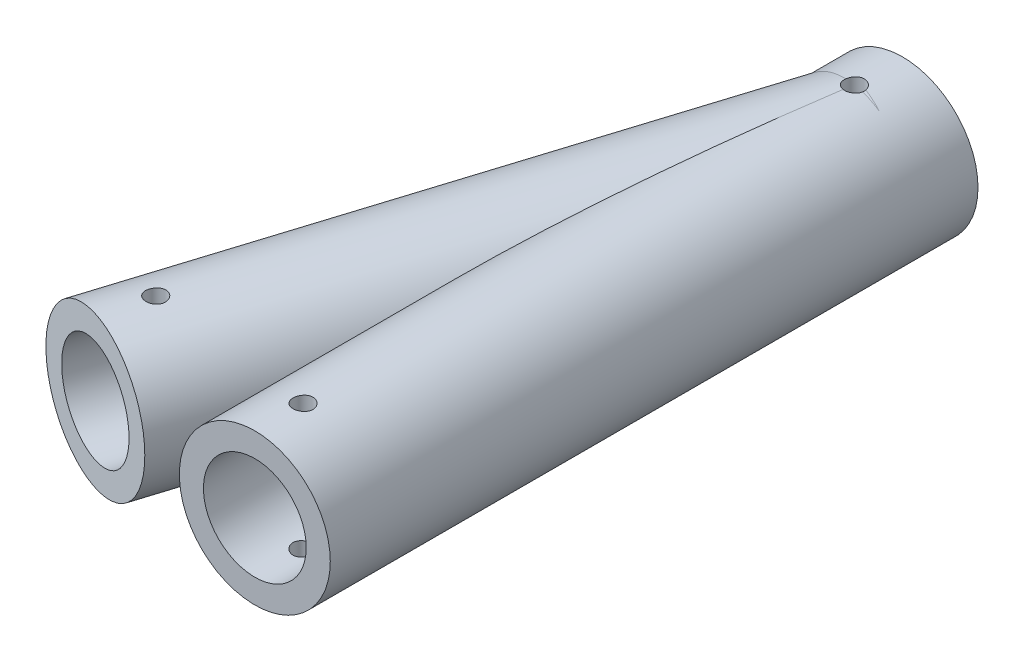
SolidWorks part; units mm, degrees
ref_plane "Front Plane" through (0, 0, 0) normal (0, 0, 1) x (1, 0, 0)
ref_plane "Top Plane" through (0, 0, 0) normal (0, 1, 0) x (1, 0, 0)
ref_plane "Right Plane" through (0, 0, 0) normal (1, 0, 0) x (0, 0, -1)
sketch "Sketch1" plane through (0, 0, 0) normal (0, 0, 1) x (1, 0, 0)
  circle A0 centre (0, 0) radius 16
  circle A1 centre (0, 0) radius 23.5
  dimension "D1" = 32
  dimension "D2" = 7.5
extrude "Boss-Extrude1" add sketch "Sketch1" along normal blind 111.7 and the other way blind 90
sketch "Sketch2" plane through (0, 0, 0) normal (0, 0, 1) x (1, 0, 0)
  line L1 (23.5, 23.5) -> (-23.5, 23.5)
  line L2 (23.5, 23.5) -> (23.5, -23.5)
  line L3 (23.5, -23.5) -> (-23.5, -23.5)
  line L4 (-23.5, 23.5) -> (-23.5, -23.5)
  line L5 (23.5, 23.5) -> (-23.5, -23.5) construction
  line L6 (23.5, -23.5) -> (-23.5, 23.5) construction
  point P0 (0, 0)
  dimension "D1" = 47
  dimension "D2" = 47
ref_plane "Plane2" through (-2.1015, 0, 6.7059) normal (-0.299, 0, 0.9542) x (0, -1, 0)
sketch "Sketch4" plane through (-2.1015, 0, 6.7059) normal (-0.299, 0, 0.9542) x (0, -1, 0)
  line L0 (-23.5, -22.4246) -> (23.5, -22.4246) construction
  circle A0 centre (0, -22.4246) radius 16
  circle A1 centre (0, -22.4246) radius 23.5
  dimension "D1" = 32
  dimension "D2" = 7.5
extrude "Boss-Extrude2" add sketch "Sketch4" along normal blind 110 and the other way blind 80
sketch "Sketch5" plane through (0, 0, -90) normal (0, 0, -1) x (-1, 0, 0)
  circle A0 centre (0, 0) radius 16
  dimension "D1" = 32
extrude "Cut-Extrude1" cut sketch "Sketch5" against normal through all
sketch "Sketch7" plane through (0, 0, 0) normal (0, 1, 0) x (1, 0, 0)
  line L0 (-23.5, -111.7) -> (23.5, -111.7) construction
  line L1 (23.5, 90) -> (-23.5, 90) construction
  line L2 (-78.8191, -97.939) -> (-33.9698, -111.9939) construction
  line L3 (0, 74.9886) -> (-56.3945, -104.9664) construction
  circle A0 centre (0, -96.7) radius 3.1
  circle A1 centre (0, 75) radius 3.1
  circle A2 centre (-51.9089, -90.6528) radius 3.1
  dimension "D1" = 6.2
  dimension "D3" = 6.2
  dimension "D5" = 6.2
  dimension "D2" = 15
  dimension "D4" = 15
  dimension "D6" = 15
extrude "Cut-Extrude3" cut sketch "Sketch7" along normal through all and the other way through all
